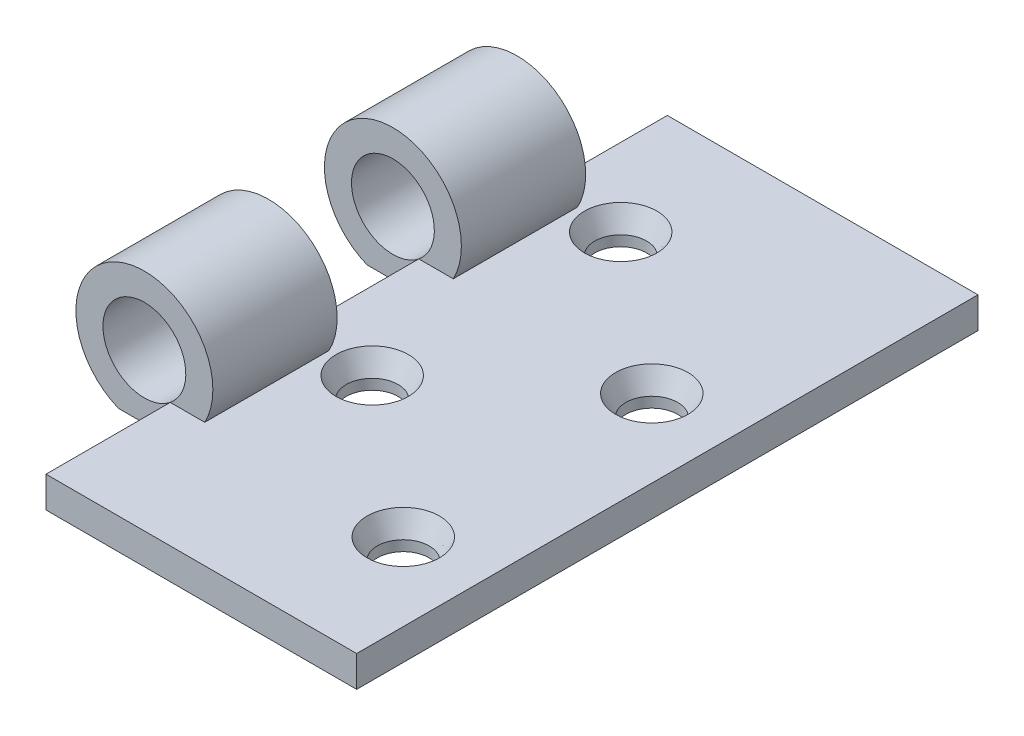
SolidWorks part; units mm, degrees
ref_plane "Front Plane" through (0, 0, 0) normal (0, 0, 1) x (1, 0, 0)
ref_plane "Top Plane" through (0, 0, 0) normal (0, 1, 0) x (1, 0, 0)
ref_plane "Right Plane" through (0, 0, 0) normal (1, 0, 0) x (0, 0, -1)
sketch "Sketch1" plane through (0, 0, 0) normal (0, 1, 0) x (1, 0, 0)
  line L1 (15, -30) -> (-15, -30)
  line L2 (15, -30) -> (15, 30)
  line L3 (15, 30) -> (-15, 30)
  line L4 (-15, -30) -> (-15, 30)
  line L5 (15, -30) -> (-15, 30) construction
  line L6 (15, 30) -> (-15, -30) construction
  point P0 (0, 0)
  dimension "D1" = 30
  dimension "D2" = 60
extrude "Boss-Extrude1" add sketch "Sketch1" along normal blind 3
sketch "Sketch2" plane through (0, 0, 30) normal (0, 0, 1) x (1, 0, 0)
  line L0 (-15, 0) -> (-20, 0)
  line L1 (-15, 3) -> (-15, 0) construction
  circle A0 centre (-17.5, 6.1225) radius 4
  arc A1 (-15, 0) -> (-20, 0) centre (-17.5, 6.1225) ccw
  dimension "D1" = 8
  dimension "D2" = 2.5
extrude "Boss-Extrude2" add sketch "Sketch2" against normal blind 12 from offset 12 offset against normal yes
mirror "Mirror1" about plane through (0, 0, 0) normal (0, 0, 1) of "Boss-Extrude2"
sketch "Sketch3" plane through (0, 0, 0) normal (0, 0, 1) x (1, 0, 0)
  line L0 (-19.7215, 0) -> (-15.2785, 0)
  line L1 (-15, 0) -> (15, 0) construction
  circle A0 centre (-17.5, 6.1225) radius 4
  arc A1 (-15.2785, 0) -> (-19.7215, 0) centre (-17.5, 6.1225) ccw
extrude "Boss-Extrude3" [suppressed] add sketch "Sketch3" along normal mid plane 12
sketch "Sketch8" plane through (0, 3, 0) normal (0, 1, 0) x (1, 0, 0)
  line L0 (7.5, 30) -> (7.5, -30) construction
  line L1 (15, 30) -> (-15, 30) construction
  line L2 (-15, -30) -> (15, -30) construction
  line L3 (7.5, -30) -> (-7.5, -30) construction
  line L4 (-7.5, -30) -> (-7.5, 30) construction
  line L5 (15, -30) -> (15, 30) construction
  circle A1 centre (7.5, -18) radius 2.5
  circle A4 centre (-7.5, -6) radius 2.5
  circle A5 centre (7.5, 6) radius 2.5
  circle A6 centre (-7.5, 18) radius 2.5
  dimension "D3" = 5
  dimension "D1" = 7.5
  dimension "D2" = 15
  dimension "D4" = 12
  dimension "D5" = 12
  dimension "D6" = 12
  dimension "D7" = 12
extrude "Cut-Extrude1" cut sketch "Sketch8" against normal through all
chamfer "Chamfer1" distance 1 distance2 2 4 edges at (7.5, 3, 20.5) (7.5, 3, -3.5) (-7.5, 3, -15.5) (-7.5, 3, 8.5)
